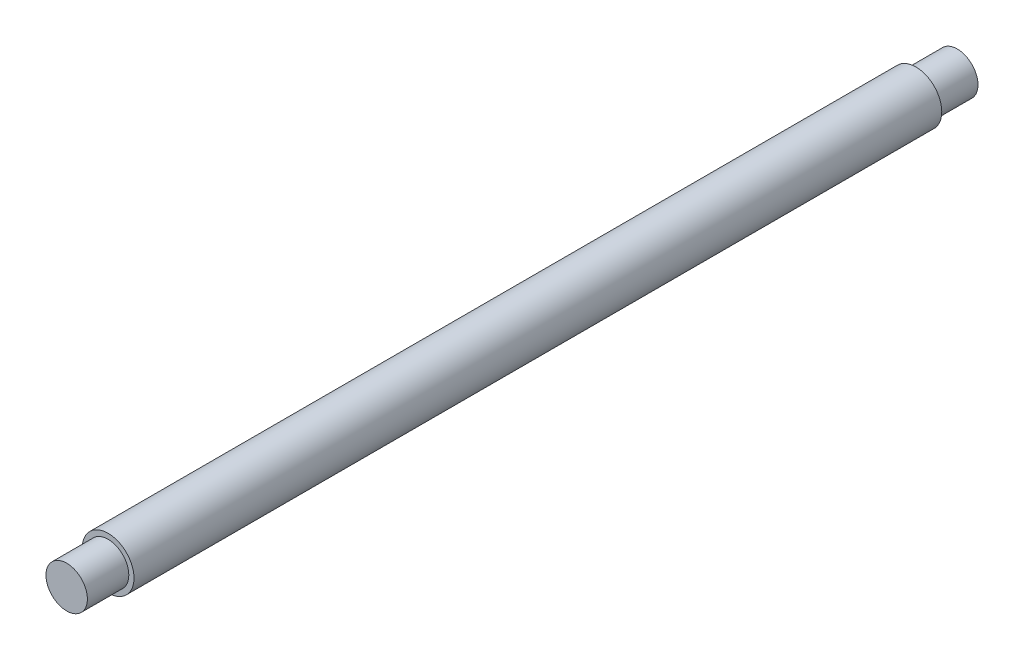
SolidWorks part; units mm, degrees
ref_plane "Front Plane" through (0, 0, 0) normal (0, 0, 1) x (1, 0, 0)
ref_plane "Top Plane" through (0, 0, 0) normal (0, 1, 0) x (1, 0, 0)
ref_plane "Right Plane" through (0, 0, 0) normal (1, 0, 0) x (0, 0, -1)
sketch "Sketch2" plane through (0, 0, 0) normal (0, 0, 1) x (1, 0, 0)
  circle A0 centre (0, 0) radius 5
  dimension "D1" = 10
extrude "Boss-Extrude1" add sketch "Sketch2" along normal mid plane 156
sketch "Sketch4" plane through (0, 0, 78) normal (0, 0, 1) x (1, 0, 0)
  circle A0 centre (0, 0) radius 4
  dimension "D1" = 8
extrude "Boss-Extrude3" add sketch "Sketch4" along normal blind 8
mirror "Mirror1" about plane through (0, 0, 0) normal (0, 0, 1) of "Boss-Extrude3"
